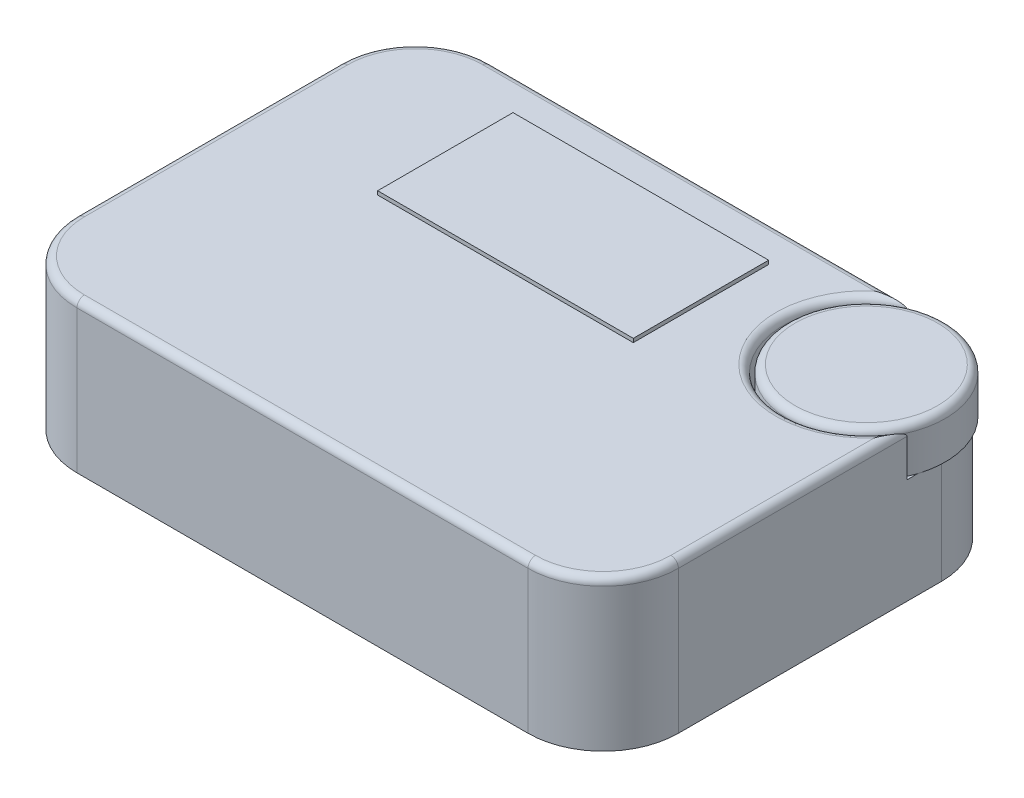
SolidWorks part; units mm, degrees
material "PVC 0.007 Plasticized"
ref_plane "Front Plane" through (0, 0, 0) normal (0, 0, 1) x (1, 0, 0)
ref_plane "Top Plane" through (0, 0, 0) normal (0, 1, 0) x (1, 0, 0)
ref_plane "Right Plane" through (0, 0, 0) normal (1, 0, 0) x (0, 0, -1)
sketch "Sketch1" plane through (0, 0, 0) normal (0, 1, 0) x (1, 0, 0)
  line L1 (-40, 27.5) -> (40, 27.5)
  line L2 (-40, 27.5) -> (-40, -27.5)
  line L3 (-40, -27.5) -> (40, -27.5)
  line L4 (40, 27.5) -> (40, -27.5)
  line L5 (-40, 27.5) -> (40, -27.5) construction
  line L6 (-40, -27.5) -> (40, 27.5) construction
  point P0 (0, 0)
  dimension "D1" = 80
  dimension "D2" = 55
extrude "Boss-Extrude2" add sketch "Sketch1" along normal blind 20
fillet "Fillet1" radius 10 4 edges at (-40, 10, -27.5) (40, 10, -27.5) (40, 10, 27.5) (-40, 10, 27.5)
sketch "Sketch3" plane through (0, 20, 0) normal (0, 1, 0) x (1, 0, 0)
  circle A0 centre (30, 17.5) radius 11
  arc A3 (40, 17.5) -> (30, 27.5) centre (30, 17.5) ccw construction
  dimension "D1" = 22
extrude "Cut-Extrude2" cut sketch "Sketch3" against normal blind 6 contours A0
sketch "Sketch5" plane through (0, 20, 0) normal (0, 1, 0) x (1, 0, 0)
  line L0 (30, 17.5) -> (-33.0282, 17.5) construction
  line L1 (-22, 22.5) -> (12, 22.5)
  line L2 (-22, 22.5) -> (-22, 4.5)
  line L3 (-22, 4.5) -> (12, 4.5)
  line L4 (12, 22.5) -> (12, 4.5)
  line L5 (-22, 22.5) -> (12, 4.5) construction
  line L6 (-22, 4.5) -> (12, 22.5) construction
  line L7 (-5, 26.8189) -> (-5, -4.6472) construction
  line L8 (25.4174, 27.5) -> (-30, 27.5) construction
  point P0 (-5, 13.5)
  dimension "D1" = 34
  dimension "D2" = 18
  dimension "D3" = 35
  dimension "D4" = 5
extrude "Cut-Extrude3" cut sketch "Sketch5" against normal blind 2
sketch "Sketch6" plane through (0, 14, 0) normal (0, 1, 0) x (1, 0, 0)
  circle A0 centre (30, 17.5) radius 10.5
  dimension "D1" = 21
extrude "Boss-Extrude3" add sketch "Sketch6" along normal up to surface (6 mm away) up to face at (-5, 20, -13.5)
fillet "Fillet2" radius 1 8 edges at (-2.2913, 20, -27.5) (-37.0711, 20, -24.5711) (-40, 20, 0) (-37.0711, 20, 24.5711) (40, 20, 2.2913) (37.0711, 20, 24.5711) (22.2218, 20, -9.7218) (0, 20, 27.5)
fillet "Fillet3" radius 1 1 edges at (30, 20, -7)
sketch "Sketch7" plane through (0, 18, 0) normal (0, 1, 0) x (1, 0, 0)
  line L1 (-22, 22.5) -> (12, 22.5)
  line L2 (-22, 22.5) -> (-22, 4.5)
  line L3 (-22, 4.5) -> (12, 4.5)
  line L4 (12, 22.5) -> (12, 4.5)
  line L5 (-22, 22.5) -> (12, 4.5) construction
  line L6 (-22, 4.5) -> (12, 22.5) construction
  line L8 (-5, 24.8509) -> (-5, -6.8196) construction
  line L9 (-22, 22.5) -> (-22, 4.5) construction
  line L10 (12, 4.5) -> (12, 22.5) construction
  line L11 (-25.0921, 13.5) -> (18.372, 13.5) construction
  line L12 (12, 22.5) -> (-22, 22.5) construction
  line L13 (-22, 4.5) -> (12, 4.5) construction
  point P0 (-5, 13.5)
  point P17 (0, 0)
  dimension "D1" = 34
  dimension "D2" = 18
extrude "Boss-Extrude4" add sketch "Sketch7" along normal blind 2.5
